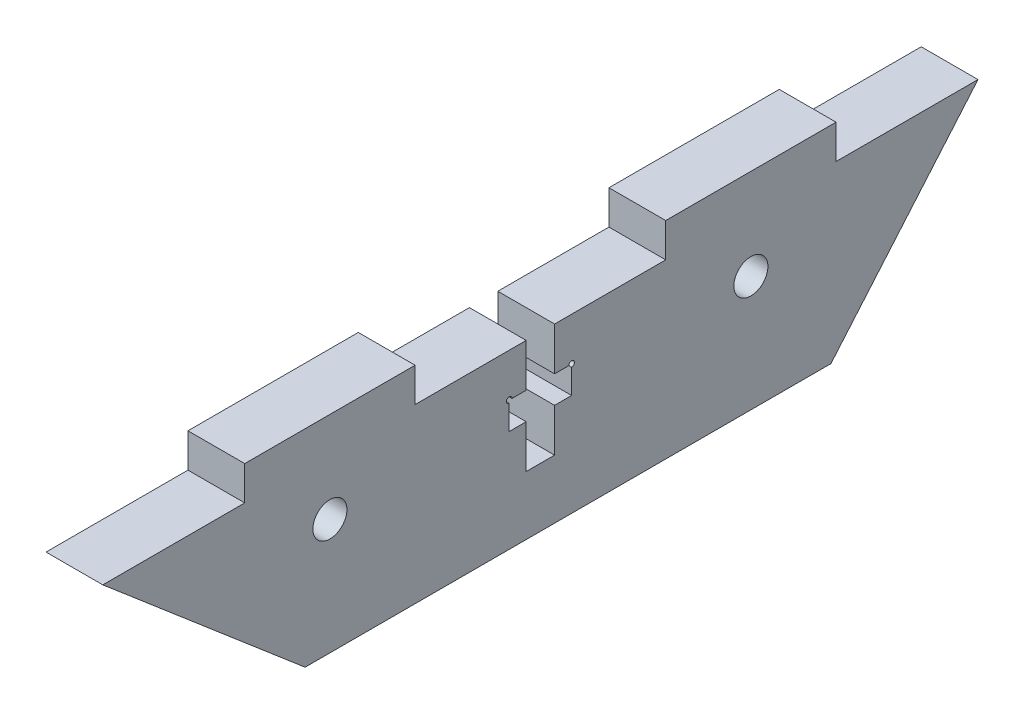
SolidWorks part; units mm, degrees
material "PMMA"
ref_plane "Front Plane" through (0, 0, 0) normal (0, 0, 1) x (1, 0, 0)
ref_plane "Top Plane" through (0, 0, 0) normal (0, 1, 0) x (1, 0, 0)
ref_plane "Right Plane" through (0, 0, 0) normal (1, 0, 0) x (0, 0, -1)
sketch "Schizzo1" plane through (0, 0, 0) normal (1, 0, 0) x (0, 0, -1)
  line L0 (-38.535, -7.595) -> (38.535, 7.595) construction
  line L1 (-38.535, 7.595) -> (38.535, 7.595)
  line L2 (-38.535, 7.595) -> (-38.535, -7.595)
  line L3 (-38.535, -7.595) -> (38.535, -7.595)
  line L4 (38.535, 7.595) -> (38.535, -7.595)
  point P4 (0, 0)
  dimension "D1" = 15.19
  dimension "D2" = 77.07
extrude "Estrusione-Estrusione1" add sketch "Schizzo1" along normal blind 5
sketch "Schizzo3" plane through (0, 0, 0) normal (1, 0, 0) x (0, 0, -1)
  line L0 (-38.535, 7.595) -> (-38.535, -7.595) construction
  line L1 (38.535, 7.595) -> (-38.535, 7.595) construction
  line L2 (38.535, -7.595) -> (38.535, 7.595) construction
  circle A0 centre (-18.535, 2.595) radius 1.5
  circle A1 centre (18.535, 2.595) radius 1.5
  dimension "D1" = 3
  dimension "D2" = 20
  dimension "D3" = 5
  dimension "D4" = 20
  dimension "D5" = 5
sketch "Schizzo2" plane through (0, 0, 0) normal (1, 0, 0) x (0, 0, -1)
  line L0 (38.535, 7.595) -> (25.5844, -7.595)
  line L1 (-38.535, -7.595) -> (38.535, -7.595) construction
  line L2 (25.5844, -7.595) -> (38.535, -7.595)
  line L3 (38.535, -7.595) -> (38.535, 7.595)
  line L4 (-38.535, 7.595) -> (-38.535, -7.595)
  line L5 (-38.535, -7.595) -> (-20.7183, -7.595)
  line L6 (-20.7183, -7.595) -> (-38.535, 7.595)
  line L7 (38.535, 7.595) -> (-38.535, 7.595) construction
  dimension "D1" = 49.55
  dimension "D2" = 40.45
extrude "Taglio-Estrusione1" cut sketch "Schizzo2" along direction (1, 0, 0) on the side of the normal through all
extrude "Taglio-Estrusione2" cut sketch "Schizzo3" along direction (1, 0, 0) on the side of the normal through all
sketch "Schizzo4" plane through (0, 7.595, 0) normal (0, 1, 0) x (1, 0, 0)
  line L0 (5, 18.535) -> (0, 18.535) construction
  line L1 (5, 38.535) -> (5, -38.535) construction
  line L2 (0, 38.535) -> (0, -38.535) construction
  line L4 (5, 38.535) -> (0, 38.535) construction
  line L6 (5, 0) -> (0, 0) construction
  line L7 (0, 26.035) -> (5, 26.035)
  line L8 (0, 26.035) -> (0, 11.035)
  line L9 (0, 11.035) -> (5, 11.035)
  line L10 (5, 26.035) -> (5, 11.035)
  line L11 (0, -26.035) -> (0, -11.035)
  line L12 (0, -26.035) -> (5, -26.035)
  line L13 (5, -26.035) -> (5, -11.035)
  line L14 (0, -11.035) -> (5, -11.035)
  point P16 (5, 18.535)
  dimension "D1" = 20
  dimension "D2" = 12.5
  dimension "D3" = 15
extrude "Estrusione-Estrusione2" add sketch "Schizzo4" along normal blind 3
sketch "Schizzo6" plane through (0, 0, 0) normal (1, 0, 0) x (0, 0, -1)
  line L0 (0, -2.405) -> (0, 7.595) construction
  line L1 (-1.25, -2.405) -> (-1.25, 1.395)
  line L2 (-1.25, 1.395) -> (-2.75, 1.395)
  line L3 (-2.75, 1.395) -> (-2.75, 3.795)
  line L4 (-2.75, 3.795) -> (-1.25, 3.795)
  line L5 (-1.25, 3.795) -> (-1.25, 7.595)
  line L6 (-1.25, 7.595) -> (1.25, 7.595)
  line L7 (1.25, 7.595) -> (1.25, 3.795)
  line L8 (1.25, 3.795) -> (2.75, 3.795)
  line L9 (2.75, 3.795) -> (2.75, 1.395)
  line L10 (2.75, 1.395) -> (1.25, 1.395)
  line L11 (1.25, 1.395) -> (1.25, -2.405)
  line L12 (1.25, -2.405) -> (-1.25, -2.405)
  line L13 (0, 7.595) -> (0, -7.595) construction
  line L14 (11.035, 7.595) -> (-11.035, 7.595) construction
  line L15 (-20.7183, -7.595) -> (25.5844, -7.595) construction
  point P14 (0, -2.405)
  dimension "D1" = 2.4
  dimension "D2" = 10
  dimension "D3" = 90
  dimension "D4" = 90
  dimension "D5" = 2.5
  dimension "D6" = 5.5
extrude "Taglio-Estrusione3" cut sketch "Schizzo6" along normal through all
sketch "Schizzo7" plane through (5, 0, 0) normal (1, 0, 0) x (0, 0, -1)
  circle A0 centre (-2.75, 3.795) radius 0.25
  circle A1 centre (2.75, 3.795) radius 0.25
  dimension "D1" = 0.5
extrude "Taglio-Estrusione4" cut sketch "Schizzo7" against normal blind 10
equation "\"Thickness5\"= 5"
equation "\"D1@Estrusione-Estrusione1\"=\"Thickness5\""
equation "\"D1@Estrusione-Estrusione2\"=\"Thickness3\""
equation "\"Thickness3\"= 3"
